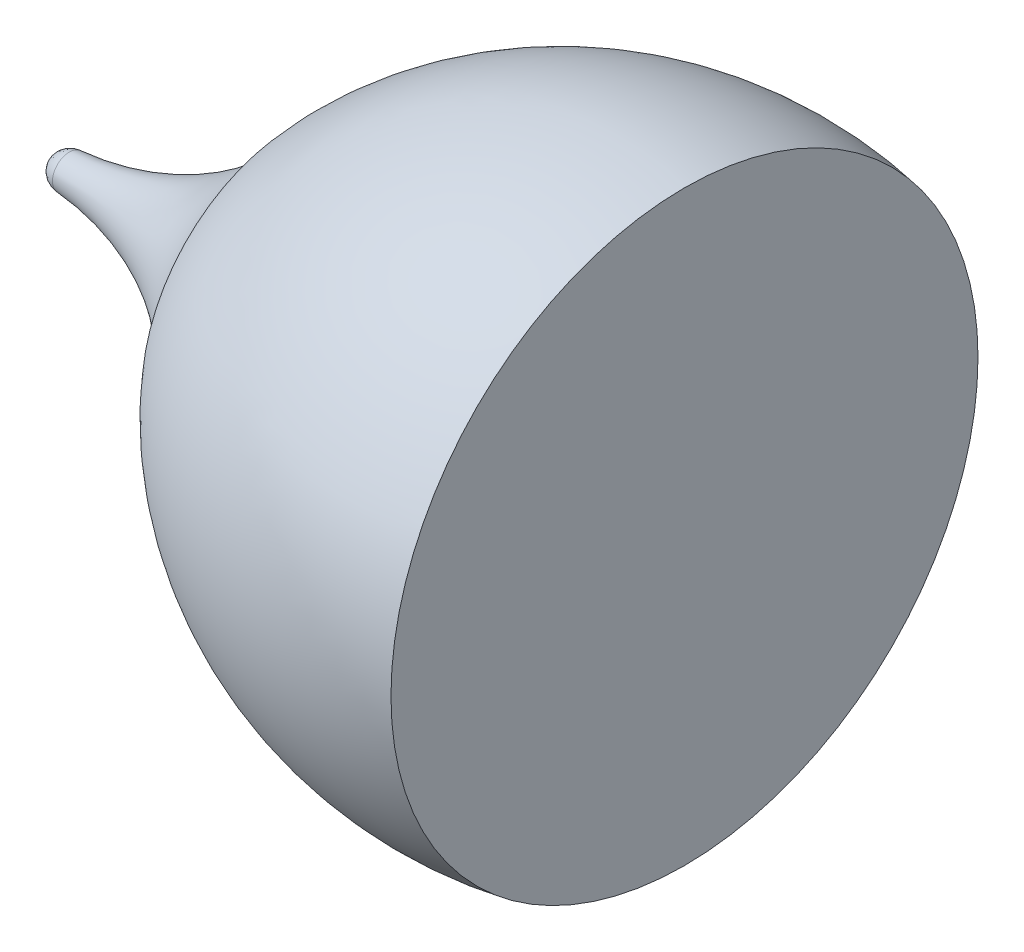
SolidWorks part; units mm, degrees
ref_plane "Front Plane" through (0, 0, 0) normal (0, 0, 1) x (1, 0, 0)
ref_plane "Top Plane" through (0, 0, 0) normal (0, 1, 0) x (1, 0, 0)
ref_plane "Right Plane" through (0, 0, 0) normal (1, 0, 0) x (0, 0, -1)
sketch "Sketch1" plane through (0, 0, 0) normal (0, 0, 1) x (1, 0, 0)
  line L0 (-39.0995, 5.1004) -> (-16.8103, 5.1004)
  line L1 (-16.8103, 5.1004) -> (-16.8103, 15.446)
  arc A0 (-16.8103, 15.446) -> (-30.4989, 10.5365) centre (-19.3833, 1.0823) ccw
  arc A2 (-39.0995, 5.1004) -> (-38.4938, 5.6951) centre (-38.4485, 5.0431) cw
  arc A3 (-30.4989, 10.5365) -> (-38.4938, 5.6951) centre (-39.2006, 15.8842) cw
revolve "Revolve1" add sketch "Sketch1" angle 360 about L0
